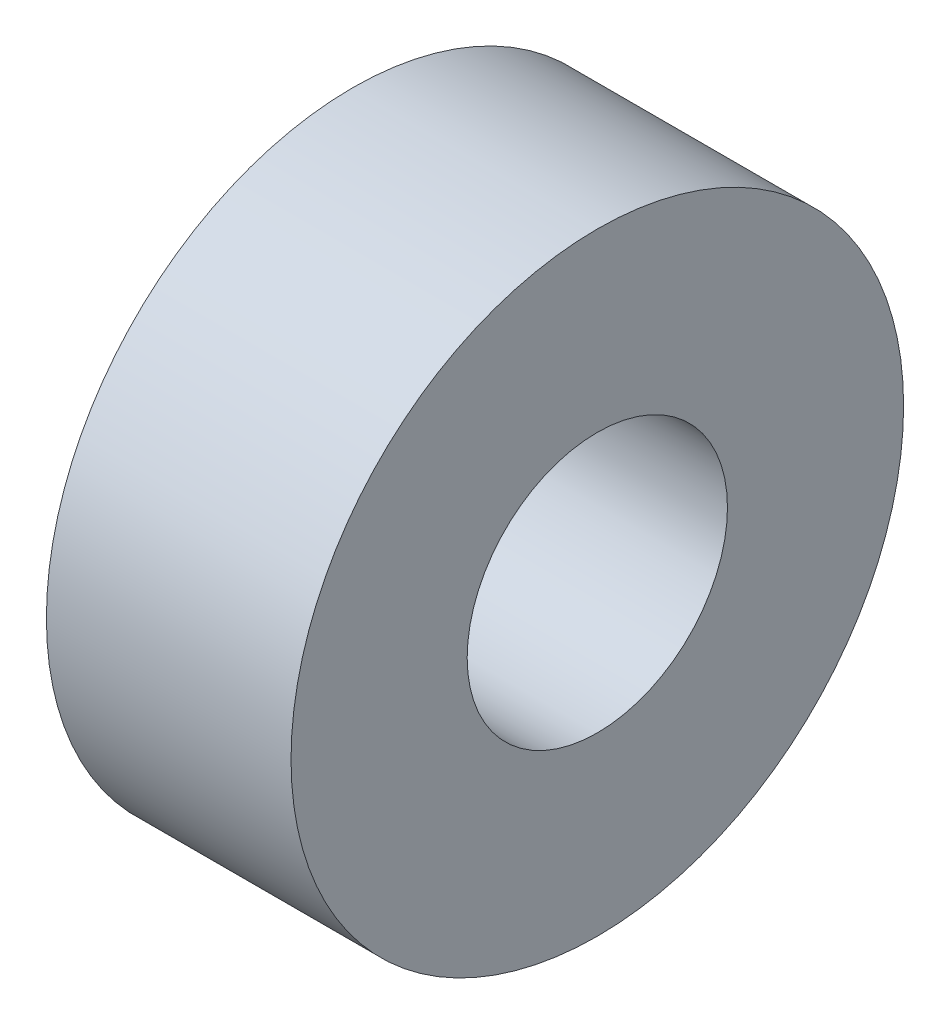
SolidWorks part; units mm, degrees
material "Delrin 2700 NC010, Low Viscosity Acetal Copolymer (SS)"
ref_plane "Front Plane" through (0, 0, 0) normal (0, 0, 1) x (1, 0, 0)
ref_plane "Top Plane" through (0, 0, 0) normal (0, 1, 0) x (1, 0, 0)
ref_plane "Right Plane" through (0, 0, 0) normal (1, 0, 0) x (0, 0, -1)
sketch "Sketch1" plane through (0, 0, 0) normal (1, 0, 0) x (0, 0, -1)
  circle A0 centre (0, 0) radius 3.3782
  circle A1 centre (0, 0) radius 7.9502
  dimension "D1" = 6.7564
  dimension "D2" = 15.9004
extrude "Boss-Extrude1" add sketch "Sketch1" along normal blind 6.35
